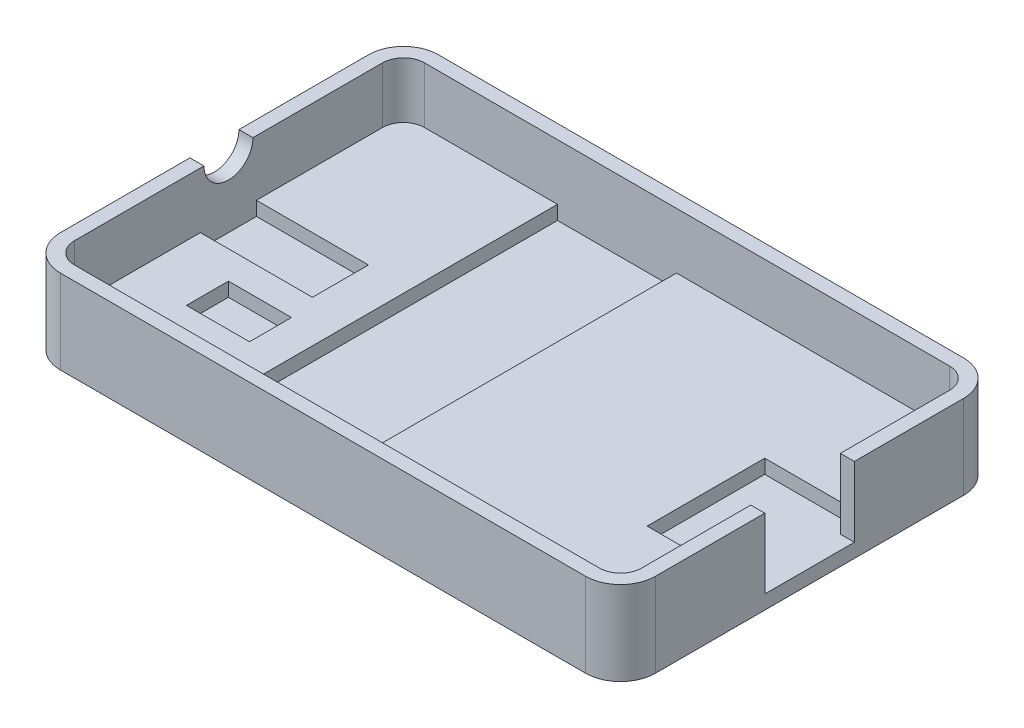
SolidWorks part; units mm, degrees
ref_plane "Front Plane" through (0, 0, 0) normal (0, 0, 1) x (1, 0, 0)
ref_plane "Top Plane" through (0, 0, 0) normal (0, 1, 0) x (1, 0, 0)
ref_plane "Right Plane" through (0, 0, 0) normal (1, 0, 0) x (0, 0, -1)
sketch "Sketch1" plane through (0, 0, 0) normal (0, 1, 0) x (1, 0, 0)
  line L1 (-21.25, 13.5) -> (21.25, 13.5)
  line L2 (-21.25, 13.5) -> (-21.25, -13.5)
  line L3 (-21.25, -13.5) -> (21.25, -13.5)
  line L4 (21.25, 13.5) -> (21.25, -13.5)
  line L5 (-21.25, 13.5) -> (21.25, -13.5) construction
  line L6 (-21.25, -13.5) -> (21.25, 13.5) construction
  point P0 (0, 0)
  dimension "D1" = 27
  dimension "D2" = 42.5
extrude "Boss-Extrude1" add sketch "Sketch1" along normal blind 6
sketch "Sketch2" plane through (0, 6, 0) normal (0, 1, 0) x (1, 0, 0)
  line L0 (-21.25, -13.5) -> (21.25, -13.5) construction
  line L1 (-20.25, 12.5) -> (20.25, 12.5)
  line L2 (-20.25, 12.5) -> (-20.25, -12.5)
  line L3 (-20.25, -12.5) -> (20.25, -12.5)
  line L4 (20.25, 12.5) -> (20.25, -12.5)
  line L5 (-20.25, 12.5) -> (20.25, -12.5) construction
  line L6 (-20.25, -12.5) -> (20.25, 12.5) construction
  line L7 (-21.25, 13.5) -> (-21.25, -13.5) construction
  point P0 (0, 0)
  dimension "D1" = 1
  dimension "D2" = 1
extrude "Cut-Extrude1" cut sketch "Sketch2" against normal blind 4
sketch "Sketch3" plane through (0, 6, 0) normal (0, 1, 0) x (1, 0, 0)
  line L0 (21.25, 0) -> (0, 0) construction
  line L1 (21.25, -13.5) -> (21.25, 13.5) construction
  line L3 (14.85, 3.2) -> (21.25, 3.2)
  line L4 (14.85, 3.2) -> (14.85, -3.2)
  line L5 (14.85, -3.2) -> (21.25, -3.2)
  line L6 (21.25, 3.2) -> (21.25, -3.2)
  line L7 (14.85, 3.2) -> (21.25, -3.2) construction
  line L8 (14.85, -3.2) -> (21.25, 3.2) construction
  point P5 (18.05, 0)
  dimension "D1" = 6.4
  dimension "D2" = 6.4
extrude "Cut-Extrude2" cut sketch "Sketch3" against normal blind 5
sketch "Sketch4" plane through (-21.25, 0, 0) normal (-1, 0, 0) x (0, 0, 1)
  line L0 (-13.5, 6) -> (13.5, 6) construction
  circle A1 centre (0, 6) radius 1.75
  dimension "D1" = 3.5
extrude "Cut-Extrude3" cut sketch "Sketch4" against normal up to next contours A1
sketch "Sketch5" plane through (0, 2, 0) normal (0, 1, 0) x (1, 0, 0)
  line L0 (20.25, 12.5) -> (-20.25, 12.5) construction
  line L1 (-9.25, 12.5) -> (-0.75, 12.5)
  line L2 (-9.25, 12.5) -> (-9.25, -12.5)
  line L3 (-9.25, -12.5) -> (-0.75, -12.5)
  line L4 (-0.75, 12.5) -> (-0.75, -12.5)
  line L5 (-20.25, -12.5) -> (20.25, -12.5) construction
  line L6 (-20.25, 12.5) -> (-20.25, 1.75) construction
  dimension "D1" = 11
  dimension "D2" = 8.5
extrude "Cut-Extrude4" cut sketch "Sketch5" against normal blind 1
sketch "Sketch6" plane through (0, 2, 0) normal (0, 1, 0) x (1, 0, 0)
  line L0 (-9.25, 0) -> (-20.25, 0)
  line L1 (-9.25, 12.5) -> (-9.25, -12.5) construction
  line L2 (-20.25, 12.5) -> (-20.25, -12.5) construction
  line L4 (-12.25, 2) -> (-20.25, 2)
  line L5 (-12.25, 2) -> (-12.25, -2)
  line L6 (-12.25, -2) -> (-20.25, -2)
  line L7 (-20.25, 2) -> (-20.25, -2)
  line L8 (-12.25, 2) -> (-20.25, -2) construction
  line L9 (-12.25, -2) -> (-20.25, 2) construction
  point P6 (-16.25, 0)
  dimension "D1" = 4
  dimension "D2" = 8
extrude "Cut-Extrude5" cut sketch "Sketch6" against normal blind 1 contours L5 L6 L7 L4
sketch "Sketch7" plane through (0, 2, 0) normal (0, 1, 0) x (1, 0, 0)
  line L0 (-20.25, -2) -> (-20.25, -12.5) construction
  line L1 (-16.25, -4) -> (-11.75, -4)
  line L2 (-16.25, -4) -> (-16.25, -7)
  line L3 (-16.25, -7) -> (-11.75, -7)
  line L4 (-11.75, -4) -> (-11.75, -7)
  line L5 (-16.25, -4) -> (-11.75, -7) construction
  line L6 (-16.25, -7) -> (-11.75, -4) construction
  line L7 (-9.25, 12.5) -> (-20.25, 12.5) construction
  point P0 (-14, -5.5)
  dimension "D1" = 4.5
  dimension "D2" = 3
  dimension "D3" = 4
  dimension "D4" = 16.5
extrude "Cut-Extrude6" cut sketch "Sketch7" against normal blind 1
fillet "Fillet1" radius 1.5 4 edges at (20.25, 4, 12.5) (-20.25, 4, 12.5) (20.25, 4, -12.5) (-20.25, 4, -12.5)
fillet "Fillet2" radius 2.5 4 edges at (-21.25, 3, -13.5) (21.25, 3, -13.5) (21.25, 3, 13.5) (-21.25, 3, 13.5)
sketch "Sketch8" plane through (0, 2, 0) normal (0, 1, 0) x (1, 0, 0)
  line L0 (20.25, 3.2) -> (20.25, 11) construction
  line L1 (13.85, -4.2) -> (20.25, -4.2)
  line L2 (13.85, -4.2) -> (13.85, 4.2)
  line L3 (13.85, 4.2) -> (20.25, 4.2)
  line L4 (20.25, -4.2) -> (20.25, 4.2)
  line L5 (13.85, -4.2) -> (20.25, 4.2) construction
  line L6 (13.85, 4.2) -> (20.25, -4.2) construction
  line L7 (14.85, -3.2) -> (21.25, -3.2) construction
  line L8 (20.25, 3.2) -> (14.85, 3.2) construction
  line L9 (14.85, 3.2) -> (14.85, -3.2) construction
  point P0 (17.05, 0)
  dimension "D1" = 1
  dimension "D2" = 1
  dimension "D3" = 1
extrude "Cut-Extrude7" cut sketch "Sketch8" against normal blind 1
